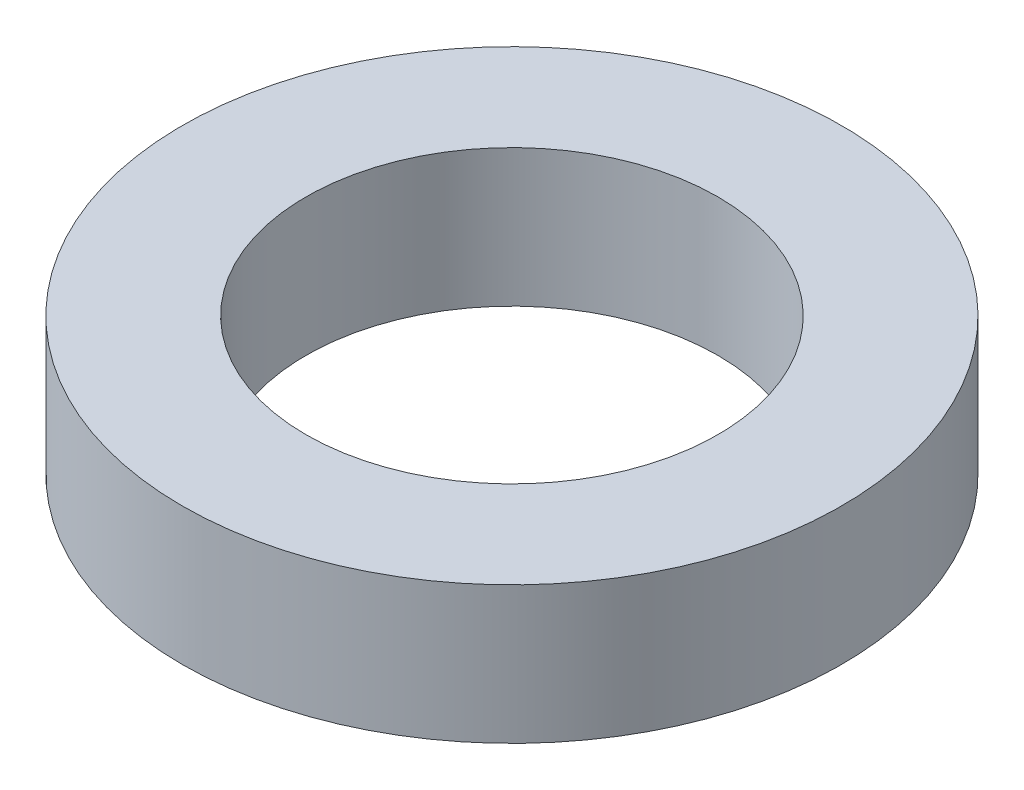
SolidWorks part; units mm, degrees
material "1023 Carbon Steel Sheet (SS)"
ref_plane "Front Plane" through (0, 0, 0) normal (0, 0, 1) x (1, 0, 0)
ref_plane "Top Plane" through (0, 0, 0) normal (0, 1, 0) x (1, 0, 0)
ref_plane "Right Plane" through (0, 0, 0) normal (1, 0, 0) x (0, 0, -1)
sketch "Sketch1" plane through (0, 0, 0) normal (0, 1, 0) x (1, 0, 0)
  circle A0 centre (0, 0) radius 12
  circle A1 centre (0, 0) radius 7.5
  dimension "D1" = 24
  dimension "D2" = 15
extrude "Boss-Extrude1" add sketch "Sketch1" along normal mid plane 5
equation "\"ID\"= 15mm"
equation "\"D2@Sketch1\"=\"ID\""
equation "\"OD\"= 24mm"
equation "\"D1@Sketch1\"=\"OD\""
equation "\"thick\"= 5mm"
equation "\"D1@Boss-Extrude1\"=\"thick\""
